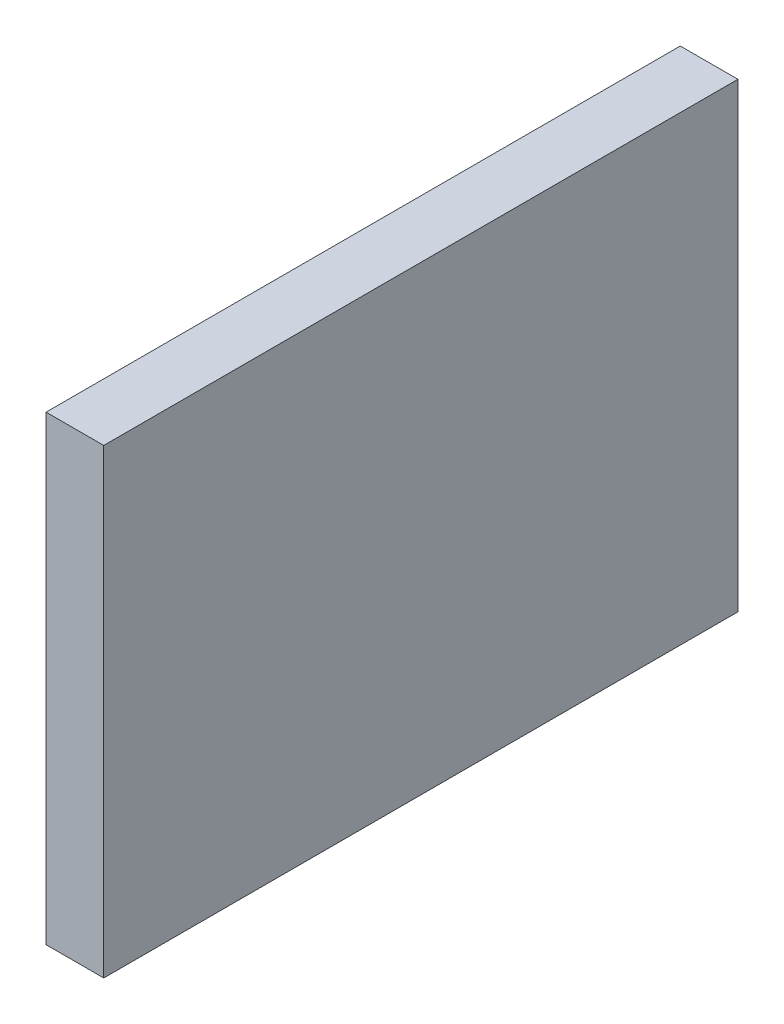
SolidWorks part; units mm, degrees
ref_plane "Front Plane" through (0, 0, 0) normal (0, 0, 1) x (1, 0, 0)
ref_plane "Top Plane" through (0, 0, 0) normal (0, 1, 0) x (1, 0, 0)
ref_plane "Right Plane" through (0, 0, 0) normal (1, 0, 0) x (0, 0, -1)
sketch "Sketch2" plane through (0, 0, 0) normal (0, 0, 1) x (1, 0, 0)
  line L1 (919.4, 560.3253) -> (944.8, 560.3253)
  line L2 (919.4, 824.2334) -> (919.4, 469.6624) construction
  line L3 (944.8, 824.2334) -> (944.8, 469.6624) construction
  line L4 (919.4, 763.5253) -> (944.8, 763.5253)
  line L5 (944.8, 763.5253) -> (944.8, 560.3253)
  line L6 (919.4, 763.5253) -> (919.4, 560.3253)
  dimension "D1" = 76.2
  dimension "D2" = 203.2
extrude "Boss-Extrude1" add sketch "Sketch2" along normal up to surface (279.4 mm away)
